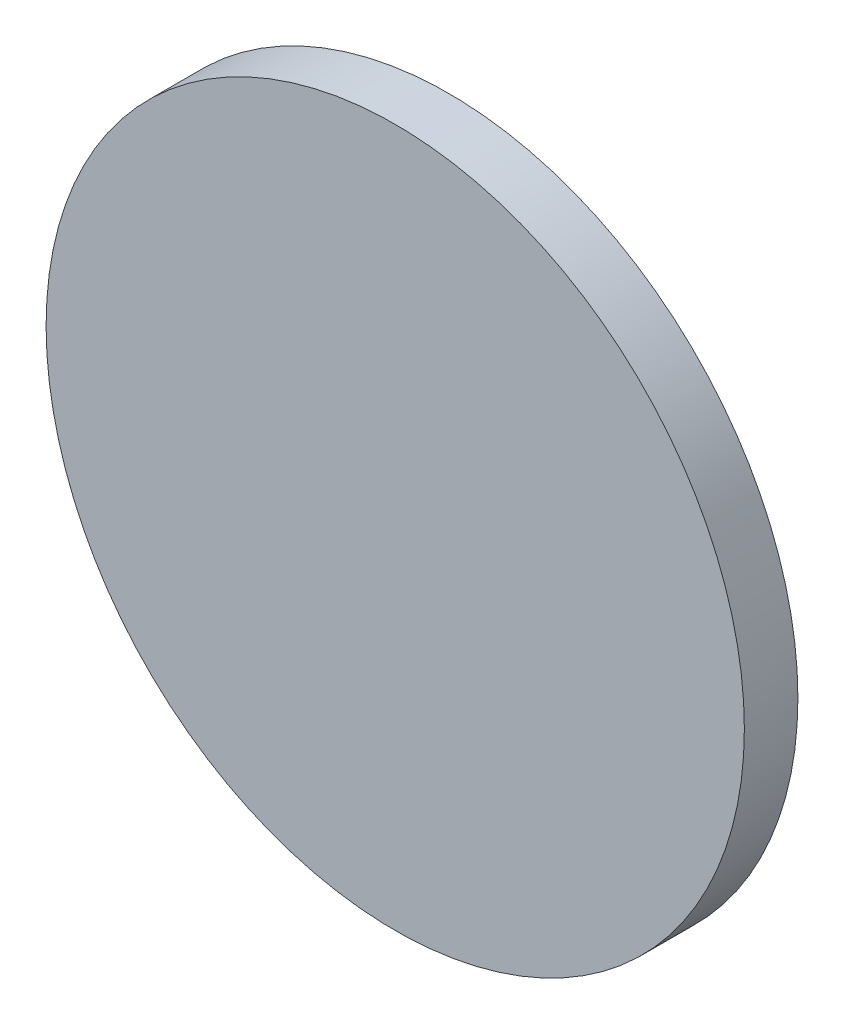
SolidWorks part; units mm, degrees
ref_plane "前视基准面" through (0, 0, 0) normal (0, 0, 1) x (1, 0, 0)
ref_plane "上视基准面" through (0, 0, 0) normal (0, 1, 0) x (1, 0, 0)
ref_plane "右视基准面" through (0, 0, 0) normal (1, 0, 0) x (0, 0, -1)
sketch "草图1" plane through (0, 0, 0) normal (0, 0, 1) x (1, 0, 0)
  circle A0 centre (108.615, 61.5632) radius 15
  dimension "D1" = 30
extrude "凸台-拉伸1" add sketch "草图1" along normal blind 2.3
